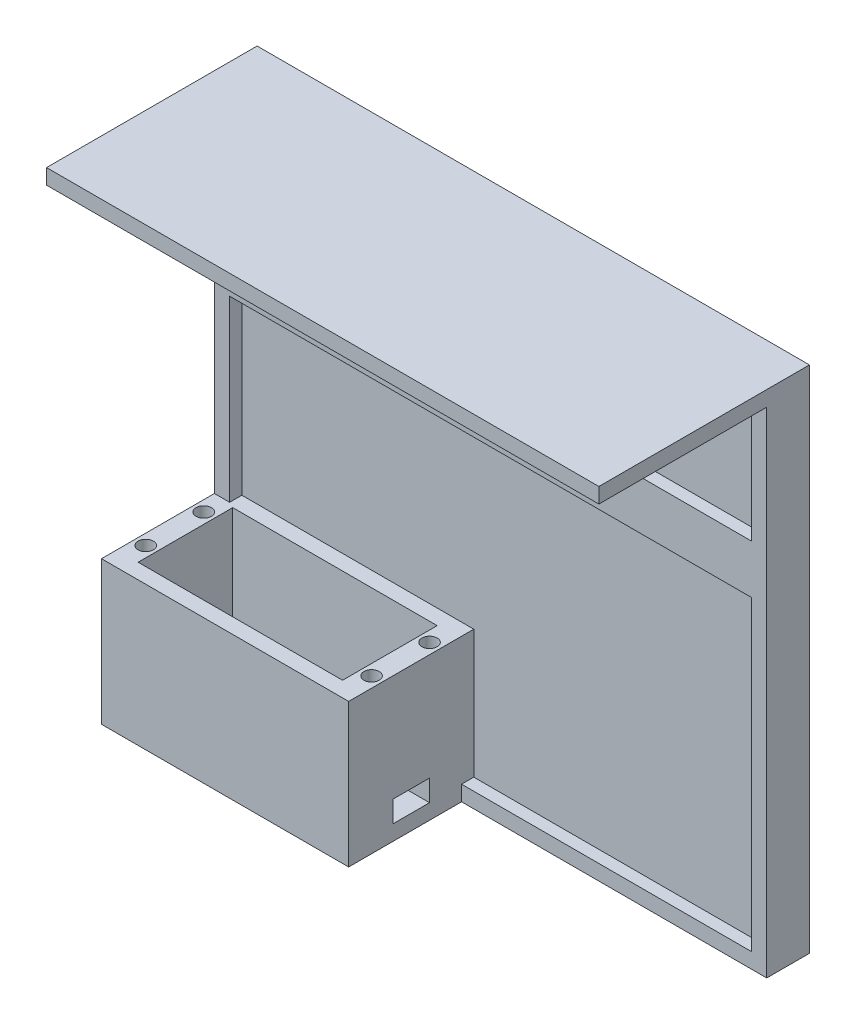
SolidWorks part; units mm, degrees
ref_plane "Front Plane" through (0, 0, 0) normal (0, 0, 1) x (1, 0, 0)
ref_plane "Top Plane" through (0, 0, 0) normal (0, 1, 0) x (1, 0, 0)
ref_plane "Right Plane" through (0, 0, 0) normal (1, 0, 0) x (0, 0, -1)
sketch "Sketch2" plane through (0, 0, 0) normal (0, 1, 0) x (1, 0, 0)
  line L1 (-33.5, -15.5) -> (33.5, -15.5)
  line L2 (-33.5, -15.5) -> (-33.5, 15.5)
  line L3 (-33.5, 15.5) -> (33.5, 15.5)
  line L4 (33.5, -15.5) -> (33.5, 15.5)
  line L5 (-33.5, -15.5) -> (33.5, 15.5) construction
  line L6 (-33.5, 15.5) -> (33.5, -15.5) construction
  line L7 (-40.5, -20.5) -> (40.5, -20.5)
  line L8 (-40.5, -20.5) -> (-40.5, 20.5)
  line L9 (-40.5, 20.5) -> (40.5, 20.5)
  line L10 (40.5, -20.5) -> (40.5, 20.5)
  line L11 (-40.5, -20.5) -> (40.5, 20.5) construction
  line L12 (-40.5, 20.5) -> (40.5, -20.5) construction
  point P0 (0, 0)
  point P6 (0, 0)
  dimension "D1" = 67
  dimension "D2" = 31
  dimension "D3" = 5
  dimension "D4" = 7
extrude "Boss-Extrude1" add sketch "Sketch2" along normal blind 42 and the other way blind 5
sketch "Sketch3" plane through (-33.5, 0, 0) normal (1, 0, 0) x (0, 0, -1)
  line L0 (15.5, -5) -> (15.5, 42) construction
  line L1 (-15.5, -5) -> (15.5, -5)
  line L2 (-15.5, -5) -> (-15.5, 0)
  line L3 (-15.5, 0) -> (15.5, 0)
  line L4 (15.5, -5) -> (15.5, 0)
  dimension "D1" = 5
extrude "Boss-Extrude2" add sketch "Sketch3" along normal up to next
sketch "Sketch4" plane through (0, 42, 0) normal (0, 1, 0) x (1, 0, 0)
  line L0 (-33.5, 15.5) -> (-33.5, -15.5) construction
  line L1 (33.5, 15.5) -> (-33.5, 15.5) construction
  circle A0 centre (-37, 9.5) radius 2.5
  circle A1 centre (-37, -9.5) radius 2.5
  dimension "D1" = 5
  dimension "D2" = 5
  dimension "D4" = 3.5
  dimension "D5" = 3.5
  dimension "D6" = 6
  dimension "D3" = 19
extrude "Cut-Extrude1" cut sketch "Sketch4" against normal through all
sketch "Sketch5" plane through (-40.5, 0, 0) normal (-1, 0, 0) x (0, 0, 1)
  line L1 (-6, 0) -> (6, 0)
  line L2 (-6, 0) -> (-6, 7)
  line L3 (-6, 7) -> (6, 7)
  line L4 (6, 0) -> (6, 7)
  dimension "D1" = 7
  dimension "D2" = 12
extrude "Cut-Extrude2" cut sketch "Sketch5" against normal blind 20
mirror "Mirror1" about plane through (0, 0, 0) normal (1, 0, 0) of "Cut-Extrude2", "Cut-Extrude1"
sketch "Sketch6" plane through (0, 0, -20.5) normal (0, 0, -1) x (-1, 0, 0)
  line L1 (-40.5, 42) -> (40.5, 42)
  line L2 (-40.5, 42) -> (-40.5, -5)
  line L3 (-40.5, -5) -> (40.5, -5)
  line L4 (40.5, 42) -> (40.5, -5)
extrude "Boss-Extrude3" add sketch "Sketch6" along normal blind 10
sketch "Sketch7" plane through (0, 42, 0) normal (0, 1, 0) x (1, 0, 0)
  line L0 (-40.5, 30.5) -> (-40.5, -20.5) construction
  line L1 (40.5, 30.5) -> (-40.5, 30.5)
  line L2 (40.5, 30.5) -> (40.5, 20.5)
  line L3 (40.5, 20.5) -> (-40.5, 20.5)
  line L4 (-40.5, 30.5) -> (-40.5, 20.5)
  dimension "D1" = 10
extrude "Boss-Extrude4" add sketch "Sketch7" along normal blind 120
sketch "Sketch9" plane through (40.5, 0, 0) normal (1, 0, 0) x (0, 0, -1)
  line L1 (30.5, -5) -> (20.5, -5)
  line L2 (30.5, -5) -> (30.5, 162)
  line L3 (30.5, 162) -> (20.5, 162)
  line L4 (20.5, -5) -> (20.5, 162)
extrude "Boss-Extrude6" add sketch "Sketch9" along normal blind 100
sketch "Sketch8" plane through (0, 0, -20.5) normal (0, 0, 1) x (1, 0, 0)
  line L0 (-40.5, 162) -> (-40.5, 42) construction
  line L1 (-40.5, 100.5) -> (140.5, 100.5)
  line L2 (-40.5, 100.5) -> (-40.5, 116.5)
  line L3 (-40.5, 116.5) -> (140.5, 116.5)
  line L4 (140.5, 100.5) -> (140.5, 116.5)
  line L10 (140.5, 162) -> (140.5, -5) construction
  line L12 (-40.5, 42) -> (40.5, 42) construction
  dimension "D1" = 58.5
  dimension "D2" = 16
extrude "Boss-Extrude5" add sketch "Sketch8" along normal blind 4
sketch "Sketch11" plane through (0, 0, -20.5) normal (0, 0, 1) x (1, 0, 0)
  line L0 (140.5, 100.5) -> (140.5, -5) construction
  line L1 (40.5, -5) -> (140.5, -5)
  line L2 (40.5, -5) -> (40.5, 0)
  line L3 (40.5, 0) -> (140.5, 0)
  line L4 (140.5, -5) -> (140.5, 0)
  line L5 (-40.5, 100.5) -> (140.5, 100.5) construction
  line L6 (140.5, -5) -> (135.5, -5)
  line L7 (140.5, -5) -> (140.5, 100.5)
  line L8 (140.5, 100.5) -> (135.5, 100.5)
  line L9 (135.5, -5) -> (135.5, 100.5)
  line L10 (-40.5, 100.5) -> (140.5, 100.5) construction
  line L11 (-40.5, 42) -> (-35.5, 42)
  line L12 (-40.5, 42) -> (-40.5, 100.5)
  line L13 (-40.5, 100.5) -> (-35.5, 100.5)
  line L14 (-35.5, 42) -> (-35.5, 100.5)
  line L15 (-40.5, 162) -> (140.5, 162) construction
  line L16 (-40.5, 116.5) -> (-35.5, 116.5)
  line L17 (-40.5, 116.5) -> (-40.5, 162)
  line L18 (-40.5, 162) -> (-35.5, 162)
  line L19 (-35.5, 116.5) -> (-35.5, 162)
  line L20 (140.5, 162) -> (140.5, 116.5) construction
  line L21 (-40.5, 162) -> (140.5, 162)
  line L22 (-40.5, 162) -> (-40.5, 157)
  line L23 (-40.5, 157) -> (140.5, 157)
  line L24 (140.5, 162) -> (140.5, 157)
  line L25 (140.5, 116.5) -> (-40.5, 116.5) construction
  line L26 (140.5, 162) -> (135.5, 162)
  line L27 (140.5, 162) -> (140.5, 116.5)
  line L28 (140.5, 116.5) -> (135.5, 116.5)
  line L29 (135.5, 162) -> (135.5, 116.5)
  line M8 (40.5, 42) -> (40.5, -5)
  line M9 (40.5, -5) -> (140.5, -5)
  line M10 (140.5, -5) -> (140.5, 100.5)
  dimension "D1" = 5
  dimension "D2" = 5
  dimension "D3" = 5
  dimension "D4" = 5
  dimension "D5" = 5
  dimension "D6" = 5
extrude "Boss-Extrude7" add sketch "Sketch11" along normal blind 4 contours L9 L3 M9 M8 | L9 L3 L8 M10 | L9 L1 L3 M10 | L17 L16 L19 L18 | L22 L21 L24 L23 | L27 L26 L29 L28 | L12 L11 L14 L13
sketch "Sketch12" plane through (0, 0, -16.5) normal (0, 0, 1) x (1, 0, 0)
  line L0 (140.5, -5) -> (140.5, 162) construction
  line L1 (-40.5, 162) -> (140.5, 162)
  line L2 (-40.5, 162) -> (-40.5, 157)
  line L3 (-40.5, 157) -> (140.5, 157)
  line L4 (140.5, 162) -> (140.5, 157)
  dimension "D1" = 5
extrude "Boss-Extrude8" add sketch "Sketch12" along normal blind 55
